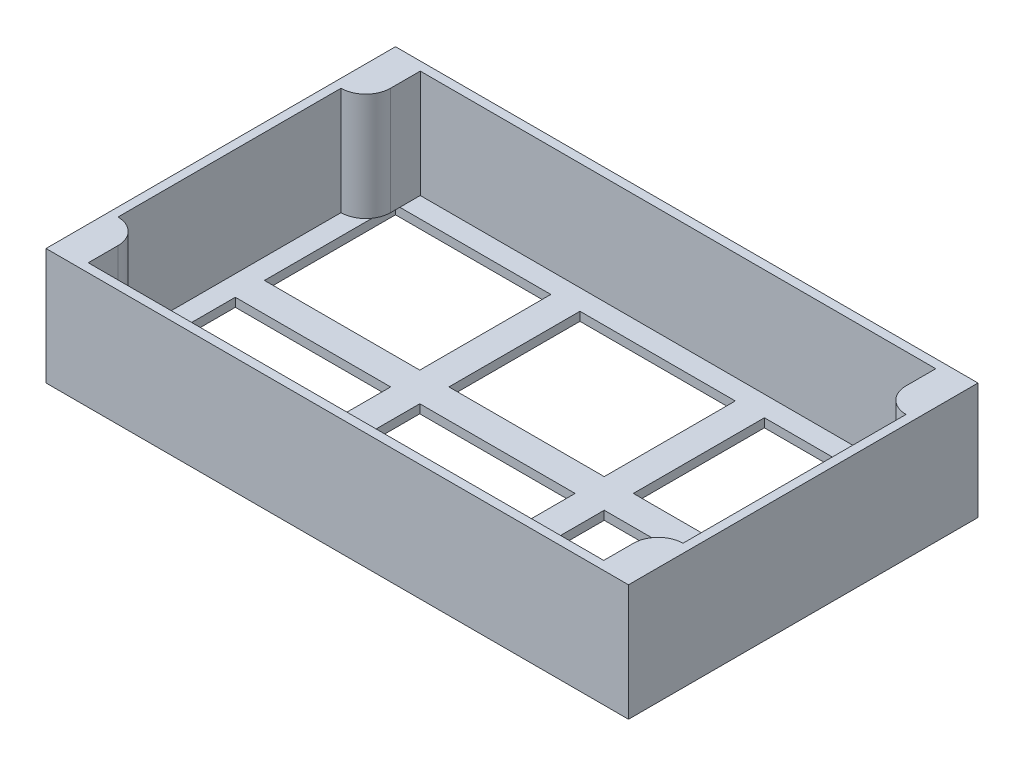
SolidWorks part; units mm, degrees
ref_plane "Front Plane" through (0, 0, 0) normal (0, 0, 1) x (1, 0, 0)
ref_plane "Top Plane" through (0, 0, 0) normal (0, 1, 0) x (1, 0, 0)
ref_plane "Right Plane" through (0, 0, 0) normal (1, 0, 0) x (0, 0, -1)
sketch "Sketch1" plane through (0, 0, 0) normal (0, 1, 0) x (1, 0, 0)
  line L0 (0, 60) -> (200, 60) construction
  line L1 (0, 0) -> (200, 0)
  line L2 (0, 0) -> (0, 120)
  line L3 (0, 120) -> (200, 120)
  line L4 (200, 0) -> (200, 120)
  line L5 (10, 110) -> (63.3333, 110)
  line L6 (10, 110) -> (10, 65)
  line L7 (10, 65) -> (63.3333, 65)
  line L8 (63.3333, 110) -> (63.3333, 65)
  line L9 (10, 10) -> (63.3333, 10)
  line L10 (10, 10) -> (10, 55)
  line L11 (10, 55) -> (63.3333, 55)
  line L12 (63.3333, 10) -> (63.3333, 55)
  line L13 (73.3333, 110) -> (126.6667, 110)
  line L14 (73.3333, 110) -> (73.3333, 65)
  line L15 (73.3333, 65) -> (126.6667, 65)
  line L16 (126.6667, 110) -> (126.6667, 65)
  line L17 (136.6667, 110) -> (190, 110)
  line L18 (136.6667, 110) -> (136.6667, 65)
  line L19 (136.6667, 65) -> (190, 65)
  line L20 (190, 110) -> (190, 65)
  line L21 (190, 10) -> (136.6667, 10)
  line L22 (190, 10) -> (190, 55)
  line L23 (190, 55) -> (136.6667, 55)
  line L24 (136.6667, 10) -> (136.6667, 55)
  line L25 (73.3333, 55) -> (126.6667, 55)
  line L26 (73.3333, 55) -> (73.3333, 10)
  line L27 (73.3333, 10) -> (126.6667, 10)
  line L28 (126.6667, 55) -> (126.6667, 10)
  line L29 (10, 65) -> (10, 55) construction
  point P31 (10, 60)
  point P32 (100, 110)
  point P33 (100, 120)
  dimension "D1" = 120
  dimension "D2" = 200
  dimension "D3" = 10
  dimension "D4" = 10
  dimension "D5" = 10
  dimension "D6" = 10
  dimension "D7" = 10
extrude "Boss-Extrude1" add sketch "Sketch1" along normal blind 3
sketch "Sketch2" plane through (0, 3, 0) normal (0, 1, 0) x (1, 0, 0)
  line L9 (0, 0) -> (0, 120)
  line L10 (0, 60) -> (3, 60) construction
  line L11 (3, 98.3) -> (3, 21.7)
  line L12 (11.5, 13.2) -> (11.5, 3)
  line L13 (0, 120) -> (0, 0) construction
  line L14 (0, 0) -> (200, 0) construction
  line L18 (11.5, 3) -> (188.5, 3)
  line L19 (100, 3) -> (100, 0) construction
  line L24 (200, 0) -> (0, 0)
  line L25 (100, 117) -> (100, 120) construction
  line L26 (200, 120) -> (0, 120)
  line L27 (11.5, 117) -> (188.5, 117)
  line L28 (11.5, 106.8) -> (11.5, 117)
  line L29 (200, 60) -> (197, 60) construction
  line L30 (188.5, 106.8) -> (188.5, 117)
  line L31 (188.5, 13.2) -> (188.5, 3)
  line L32 (197, 98.3) -> (197, 21.7)
  line L33 (200, 0) -> (200, 120)
  arc A4 (3, 21.7) -> (11.5, 13.2) centre (3, 13.2) cw
  arc A5 (3, 98.3) -> (11.5, 106.8) centre (3, 106.8) ccw
  arc A6 (197, 98.3) -> (188.5, 106.8) centre (197, 106.8) cw
  arc A7 (197, 21.7) -> (188.5, 13.2) centre (197, 13.2) ccw
  point P21 (0, 60)
  point P24 (100, 0)
  dimension "D1" = 3
  dimension "D2" = 8.5
  dimension "D3" = 18.7
extrude "Boss-Extrude2" add sketch "Sketch2" along direction (0, -1, 0) on the side of the normal offset from surface (37 mm away) 40
